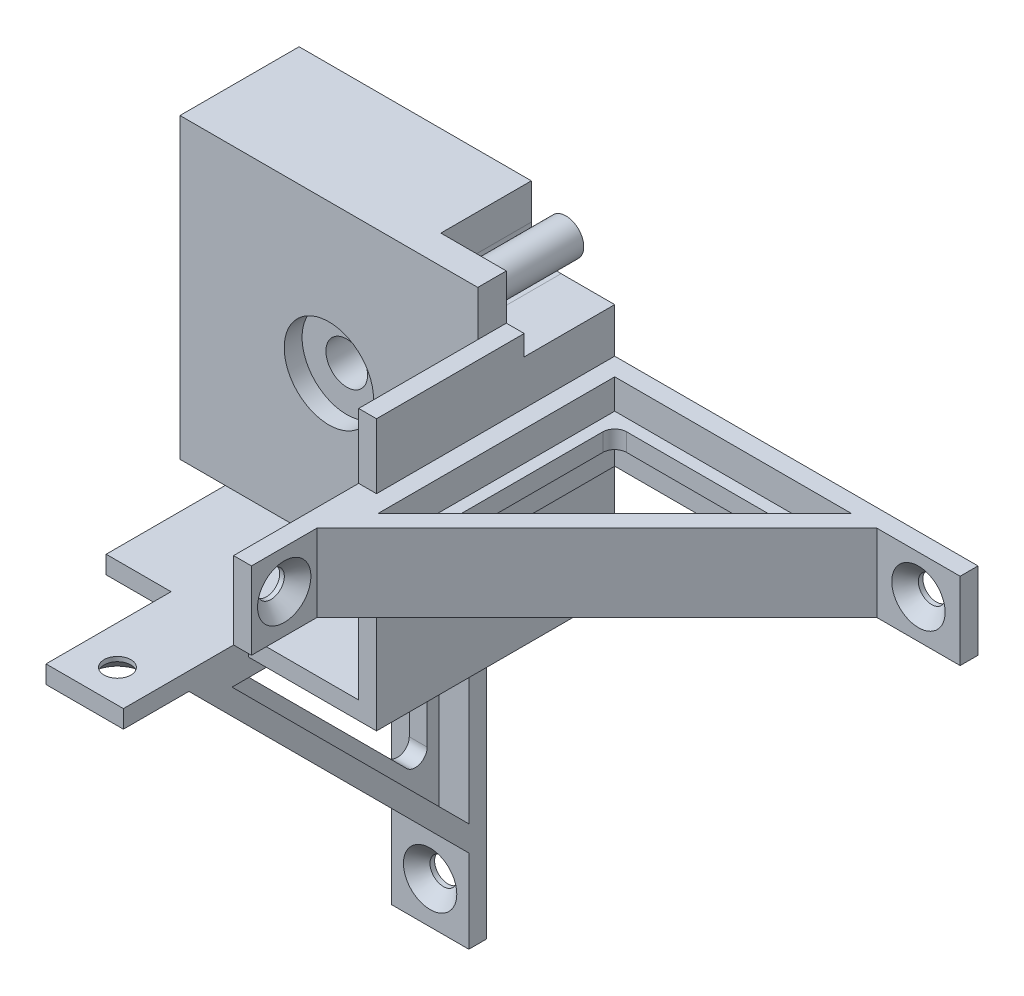
SolidWorks part; units mm, degrees
ref_plane "Alzado" through (0, 0, 0) normal (0, 0, 1) x (1, 0, 0)
ref_plane "Planta" through (0, 0, 0) normal (0, 1, 0) x (1, 0, 0)
ref_plane "Vista lateral" through (0, 0, 0) normal (1, 0, 0) x (0, 0, -1)
sketch "Croquis2" plane through (0, 0, 0) normal (0, 0, 1) x (1, 0, 0)
  line L1 (-25, -25) -> (25, -25)
  line L2 (-25, -25) -> (-25, 25)
  line L3 (-25, 25) -> (25, 25)
  line L4 (25, -25) -> (25, 25)
  line L5 (-25, -25) -> (25, 25) construction
  line L6 (-25, 25) -> (25, -25) construction
  circle A0 centre (0, 0) radius 3.5
  point P0 (0, 0)
  dimension "D3" = 7
  dimension "D1" = 50
  dimension "D2" = 50
extrude "Saliente-Extruir2" add sketch "Croquis2" along normal blind 20
sketch "Croquis3" plane through (0, 0, 20) normal (0, 0, 1) x (1, 0, 0)
  circle A0 centre (0, 0) radius 7.5
  dimension "D1" = 15
extrude "Cortar-Extruir1" cut sketch "Croquis3" against normal blind 3
sketch "Croquis4" plane through (0, 0, 0) normal (0, 0, -1) x (-1, 0, 0)
  line L0 (-25, -25) -> (-25, 17.4)
  line L1 (-25, -25) -> (-25, 25) construction
  line L2 (-25, -25) -> (17.4, -25)
  line L3 (25, -25) -> (-25, -25) construction
  line L4 (-25, 17.4) -> (-28, 17.4)
  line L5 (-28, 17.4) -> (-28, -28)
  line L6 (17.4, -25) -> (17.4, -28)
  line L7 (17.4, -28) -> (-28, -28)
  dimension "D1" = 7.6
  dimension "D2" = 7.6
  dimension "D3" = 3
  dimension "D4" = 3
extrude "Saliente-Extruir3" add sketch "Croquis4" against normal blind 40
sketch "Croquis5" plane through (0, 17.4, 0) normal (0, 1, 0) x (1, 0, 0)
  line L0 (25, 0) -> (51, 0)
  line L1 (25, 0) -> (25, -25)
  line L2 (25, -40) -> (25, -20) construction
  line L3 (25, -25) -> (51, 0)
  dimension "D1" = 26
extrude "Saliente-Extruir4" add sketch "Croquis5" against normal blind 2.65
sketch "Croquis6" plane through (0, 14.75, 0) normal (0, -1, 0) x (1, 0, 0)
  line L0 (38.2557, 12.2542) -> (37.5626, 11.5333) construction
  line L1 (28, 22.1154) -> (51, 0) construction
  line L2 (44.825, 4.5503) -> (30.3002, 18.5164)
  line L3 (44.825, 4.5503) -> (40.5623, 0.1171)
  line L4 (40.5623, 0.1171) -> (26.0376, 14.0833)
  line L5 (26.0376, 14.0833) -> (30.3002, 18.5164)
  line L6 (51, 0) -> (25.5113, 24.5083) construction
  point P6 (37.5626, 11.5333)
  point P13 (38.2557, 12.2542)
  dimension "D1" = 1
  dimension "D2" = 20.15
  dimension "D3" = 6.15
  dimension "D4" = 35.36
extrude "Cortar-Extruir2" cut sketch "Croquis6" against normal blind 2 and the other way blind 3
ref_plane "Plano1" through (0, 0, 0) normal (0.7071, 0.7071, 0) x (0.7071, -0.7071, 0)
mirror "Simetría2" about plane through (0, 0, 0) normal (0.7071, 0.7071, 0) of "Cortar-Extruir2", "Saliente-Extruir4"
sketch "Croquis11" plane through (0, 14.75, 0) normal (0, -1, 0) x (1, 0, 0)
  line L0 (28, 0) -> (51, 0)
  line L1 (51, 0) -> (28, 22.1154)
  line L2 (28, 22.1154) -> (28, 0)
extrude "Cortar-Extruir5" cut sketch "Croquis11" against normal up to vertex
sketch "Croquis14" plane through (0, 16.75, 0) normal (0, -1, 0) x (1, 0, 0)
  line L6 (26.0376, 14.0833) -> (28, 12.1963)
  line L7 (28, 12.1963) -> (28, 16.1242)
  line L8 (28, 16.1242) -> (26.0376, 14.0833)
  line L9 (26.0376, 14.0833) -> (28, 12.1963)
  line L10 (28, 12.1963) -> (28, 16.1242)
  line L11 (28, 16.1242) -> (26.0376, 14.0833)
  dimension "D1" = 0
extrude "Saliente-Extruir5" add sketch "Croquis14" along normal up to vertex (44.75 mm away)
sketch "Croquis13" plane through (0, 0, 0) normal (0, 0, -1) x (-1, 0, 0)
  line L0 (-25, 25) -> (-14, 25)
  line L1 (-25, 25) -> (25, 25) construction
  line L2 (-25, 25) -> (-25, 17.4)
  line L3 (-25, 17.4) -> (-25, 25) construction
  line L4 (-25, 14) -> (-19, 14)
  line L5 (-14, 19) -> (-14, 25)
  line L6 (-25, 25) -> (-19.8028, 19.8028) construction
  line L7 (-25, 14) -> (-28, 14)
  line L8 (-28, 17.4) -> (-28, -28) construction
  line L9 (-28, 14) -> (-28, 17.4)
  line L10 (-28, 17.4) -> (-25, 17.4)
  arc A0 (-19, 14) -> (-14, 19) centre (-19, 19) ccw
  circle A1 centre (-19.8028, 19.8028) radius 3
  dimension "D3" = 5
  dimension "D6" = 6
  dimension "D1" = 11
  dimension "D2" = 11
  dimension "D4" = 7.35
  dimension "D5" = 45
extrude "Cortar-Extruir6" cut sketch "Croquis13" against normal blind 15.2
sketch "Croquis15" plane through (0, -28, 0) normal (0, -1, 0) x (1, 0, 0)
  line L0 (28, 0) -> (78, 0)
  line L1 (28, 0) -> (28, 40)
  line L2 (28, 50) -> (75, 3)
  line L3 (31, 42.7574) -> (70.7574, 3)
  line L4 (31, 3) -> (70.7574, 3)
  line L5 (31, 3) -> (31, 42.7574)
  line L6 (75, 3) -> (89, 3)
  line L7 (89, 3) -> (89, 0)
  line L8 (89, 0) -> (78, 0)
  line L9 (28, 50) -> (28, 61)
  line L10 (28, 50) -> (78, 0) construction
  line L11 (28, 40) -> (25, 40)
  line L12 (25, 40) -> (25, 61)
  line L13 (25, 61) -> (28, 61)
  line L15 (28, 0) -> (28, 50) construction
  dimension "D1" = 50
  dimension "D2" = 50
  dimension "D4" = 11
  dimension "D5" = 11
  dimension "D3" = 3
extrude "Saliente-Extruir6" add sketch "Croquis15" against normal blind 13 from offset 21.5 offset against normal yes
sketch "Croquis16" plane through (0, -6.5, 0) normal (0, -1, 0) x (1, 0, 0)
  line L3 (33, 5) -> (65.9289, 5)
  line L4 (65.9289, 5) -> (33, 37.9289)
  line L5 (33, 37.9289) -> (33, 5)
  line L6 (31, 3) -> (70.7574, 3)
  line L7 (70.7574, 3) -> (31, 42.7574)
  line L8 (31, 42.7574) -> (31, 3)
  line L9 (31, 3) -> (70.7574, 3)
  line L10 (70.7574, 3) -> (31, 42.7574)
  line L11 (31, 42.7574) -> (31, 3)
  dimension "D1" = 0
  dimension "D2" = 2
extrude "Saliente-Extruir7" add sketch "Croquis16" against normal blind 3 from offset 5 offset against normal yes
fillet "Redondeo1" radius 2 3 edges at (33, 0, 37.9289) (65.9289, 0, 5) (33, 0, 5)
sketch "Croquis17" plane through (0, 0, 3) normal (0, 0, 1) x (1, 0, 0)
  circle A0 centre (82, 0) radius 2
  dimension "D1" = 4
extrude "Cortar-Extruir7" cut sketch "Croquis17" against normal up to vertex (3 mm away)
sketch "Croquis18" plane through (28, 0, 0) normal (1, 0, 0) x (0, 0, -1)
  circle A0 centre (-55.5, 0) radius 2
  dimension "D1" = 4
extrude "Cortar-Extruir8" cut sketch "Croquis18" against normal up to vertex (3 mm away)
hole_wizard "Refrentado para tornillo tapón con cabeza plana de clavija de M42" positions "Croquis19" profile "Croquis20" countersink size "M4" standard "Ansi Metric" end condition through all
sketch "Croquis19" plane through (28, 0, 0) normal (1, 0, 0) x (0, 0, -1)
  point P0 (-55.5, 0)
sketch "Croquis20" plane through (28, 0, 55.5) normal (0, 1, 0) x (0, 0, -1)
  line L0 (0, 0) -> (0, 53)
  line L1 (0, 53) -> (2.25, 53)
  line L2 (2.25, 53) -> (2.25, 2.23)
  line L3 (2.25, 2.23) -> (4.48, 0)
  line L5 (4.48, 0) -> (0, 0)
  line L6 (-2.25, 2.23) -> (-4.48, 0) construction
  line L11 (0, -6.35) -> (0, 107.95) construction
  dimension "Diámetro de taladro hasta el siguiente" = 4.5
  dimension "Profundidad de taladro hasta el siguiente" = 53
  dimension "Diámetro de avellanado cercano" = 8.96
  dimension "Ángulo de avellanado cercano" = 90
hole_wizard "Refrentado para tornillo tapón con cabeza plana de clavija de M43" positions "Croquis21" profile "Croquis22" countersink size "M4" standard "Ansi Metric" end condition through all
sketch "Croquis21" plane through (0, 0, 3) normal (0, 0, 1) x (1, 0, 0)
  point P0 (82, 0)
sketch "Croquis22" plane through (82, 0, 3) normal (1, 0, 0) x (0, -1, 0)
  line L0 (0, 0) -> (0, 3)
  line L1 (0, 3) -> (2.25, 3)
  line L2 (2.25, 3) -> (2.25, 2.23)
  line L3 (2.25, 2.23) -> (4.48, 0)
  line L5 (4.48, 0) -> (0, 0)
  line L6 (-2.25, 2.23) -> (-4.48, 0) construction
  line L11 (0, -6.35) -> (0, 107.95) construction
  dimension "Diámetro de taladro hasta el siguiente" = 4.5
  dimension "Profundidad de taladro hasta el siguiente" = 3
  dimension "Diámetro de avellanado cercano" = 8.96
  dimension "Ángulo de avellanado cercano" = 90
mirror "Simetría3" about plane through (0, 0, 0) normal (0.7071, 0.7071, 0) of "Saliente-Extruir7", "Redondeo1", "Cortar-Extruir7", "Cortar-Extruir8", "Refrentado para tornillo tapón con cabeza plana de clavija de M42", "Refrentado para tornillo tapón con cabeza plana de clavija de M43", "Saliente-Extruir6"
